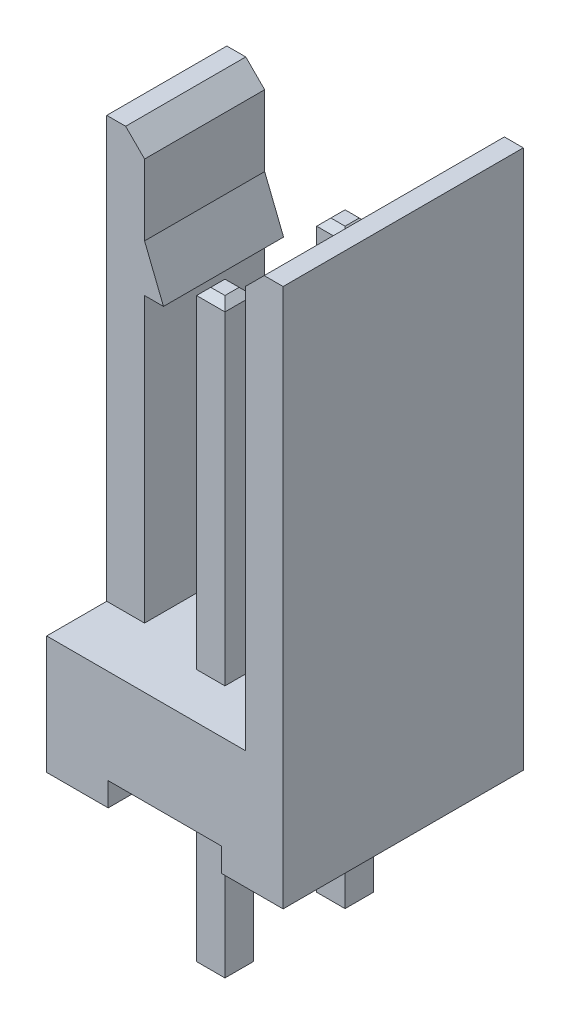
SolidWorks part; units mm, degrees
ref_plane "Plan de face" through (0, 0, 0) normal (0, 0, 1) x (1, 0, 0)
ref_plane "Plan de dessus" through (0, 0, 0) normal (0, 1, 0) x (1, 0, 0)
ref_plane "Plan de droite" through (0, 0, 0) normal (1, 0, 0) x (0, 0, -1)
sketch "Esquisse1" plane through (0, 0, 0) normal (0, 0, 1) x (1, 0, 0)
  line L0 (0, 11.4) -> (0, 0)
  line L1 (0, 0) -> (5, 0)
  line L2 (5, 0) -> (5, 11.4)
  line L3 (5, 11.4) -> (4.2, 11.4)
  line L4 (4.2, 11.4) -> (4.2, 2.5)
  line L5 (4.2, 2.5) -> (0.8, 2.5)
  line L6 (0.8, 2.5) -> (0.8, 11.4)
  line L10 (0.8, 11.4) -> (0, 11.4)
  dimension "D1" = 2.5
  dimension "D2" = 5
  dimension "D3" = 11.4
  dimension "D4" = 0.8
  dimension "D5" = 0.8
extrude "Boss.-Extru.1" add sketch "Esquisse1" along normal blind 5.08
sketch "Esquisse3" plane through (0, 11.4, 0) normal (0, 1, 0) x (1, 0, 0)
  line L0 (0.8, -5.08) -> (0.8, 0) construction
  line L1 (0, 0) -> (0.8, 0)
  line L2 (0, 0) -> (0, -1.27)
  line L3 (0, -1.27) -> (0.8, -1.27)
  line L4 (0.8, 0) -> (0.8, -1.27)
  line L6 (0, -5.08) -> (0.8, -5.08)
  line L7 (0, -5.08) -> (0, -3.81)
  line L8 (0, -3.81) -> (0.8, -3.81)
  line L9 (0.8, -5.08) -> (0.8, -3.81)
  dimension "D1" = 1.27
extrude "Enlèv. mat.-Extru.1" cut sketch "Esquisse3" against normal up to surface (8.9 mm away) up to face at (2.5, 2.5, 2.54)
sketch "Esquisse4" plane through (0, 0, 5.08) normal (0, 0, 1) x (1, 0, 0)
  line L0 (0, 0) -> (5, 0) construction
  line L1 (1.3, 0) -> (3.7, 0)
  line L2 (1.3, 0) -> (1.3, 0.5)
  line L3 (1.3, 0.5) -> (3.7, 0.5)
  line L4 (3.7, 0) -> (3.7, 0.5)
  line L5 (0, 2.5) -> (0, 0) construction
  line L6 (5, 0) -> (5, 11.4) construction
  point P8 (0, 1.25)
  dimension "D1" = 0.5
  dimension "D2" = 1.3
  dimension "D3" = 1.3
extrude "Enlèv. mat.-Extru.2" cut sketch "Esquisse4" against normal through all
sketch "Esquisse2" plane through (0, 0.5, 0) normal (0, -1, 0) x (1, 0, 0)
  line L0 (2.5, 3.81) -> (2.5, 5.08) construction
  line L1 (2.2, 3.51) -> (2.8, 3.51)
  line L2 (2.2, 3.51) -> (2.2, 4.11)
  line L3 (2.2, 4.11) -> (2.8, 4.11)
  line L4 (2.8, 3.51) -> (2.8, 4.11)
  line L5 (2.2, 3.51) -> (2.8, 4.11) construction
  line L6 (2.2, 4.11) -> (2.8, 3.51) construction
  line L7 (2.2, 0.97) -> (2.8, 0.97)
  line L8 (2.2, 0.97) -> (2.2, 1.57)
  line L9 (2.2, 1.57) -> (2.8, 1.57)
  line L10 (2.8, 0.97) -> (2.8, 1.57)
  line L11 (2.2, 0.97) -> (2.8, 1.57) construction
  line L12 (2.2, 1.57) -> (2.8, 0.97) construction
  line L16 (2.5, 1.27) -> (2.5, 0) construction
  line L18 (3.7, 5.08) -> (1.3, 5.08) construction
  line L19 (3.7, 0) -> (1.3, 0) construction
  point P0 (2.5, 3.81)
  point P5 (2.5, 1.27)
  dimension "D1" = 0.6
  dimension "D2" = 2.54
extrude "Boss.-Extru.2" add sketch "Esquisse2" along normal blind 3.5 and the other way blind 9
sketch "Esquisse5" plane through (0, 0, 3.81) normal (0, 0, 1) x (1, 0, 0)
  line L0 (0.8, 9.5) -> (1.2, 8.5)
  line L1 (0.8, 2.5) -> (0.8, 11.4) construction
  line L2 (1.2, 8.5) -> (0.8, 8.5)
  line L3 (0.8, 8.5) -> (0.8, 9.5)
  line L4 (2.8, 9.5) -> (2.2, 9.5) construction
  dimension "D1" = 1
  dimension "D2" = 0.4
extrude "Boss.-Extru.3" add sketch "Esquisse5" against normal up to surface (2.54 mm away) up to face at (0.4, 6.95, 1.27)
chamfer "Chanfrein4" distance 0.15 angle 45 16 edges at (2.5, -3, 3.51) (2.2, -3, 3.81) (2.5, -3, 4.11) (2.8, -3, 3.81) (2.5, -3, 0.97) (2.2, -3, 1.27) (2.5, -3, 1.57) (2.8, -3, 1.27) (2.5, 9.5, 4.11) (2.2, 9.5, 3.81) (2.5, 9.5, 3.51) (2.8, 9.5, 3.81) (2.5, 9.5, 1.57) (2.2, 9.5, 1.27) (2.5, 9.5, 0.97) (2.8, 9.5, 1.27)
chamfer "Chanfrein5" distance 0.4 angle 45 2 edges at (4.2, 11.4, 2.54) (0.8, 11.4, 2.54)
